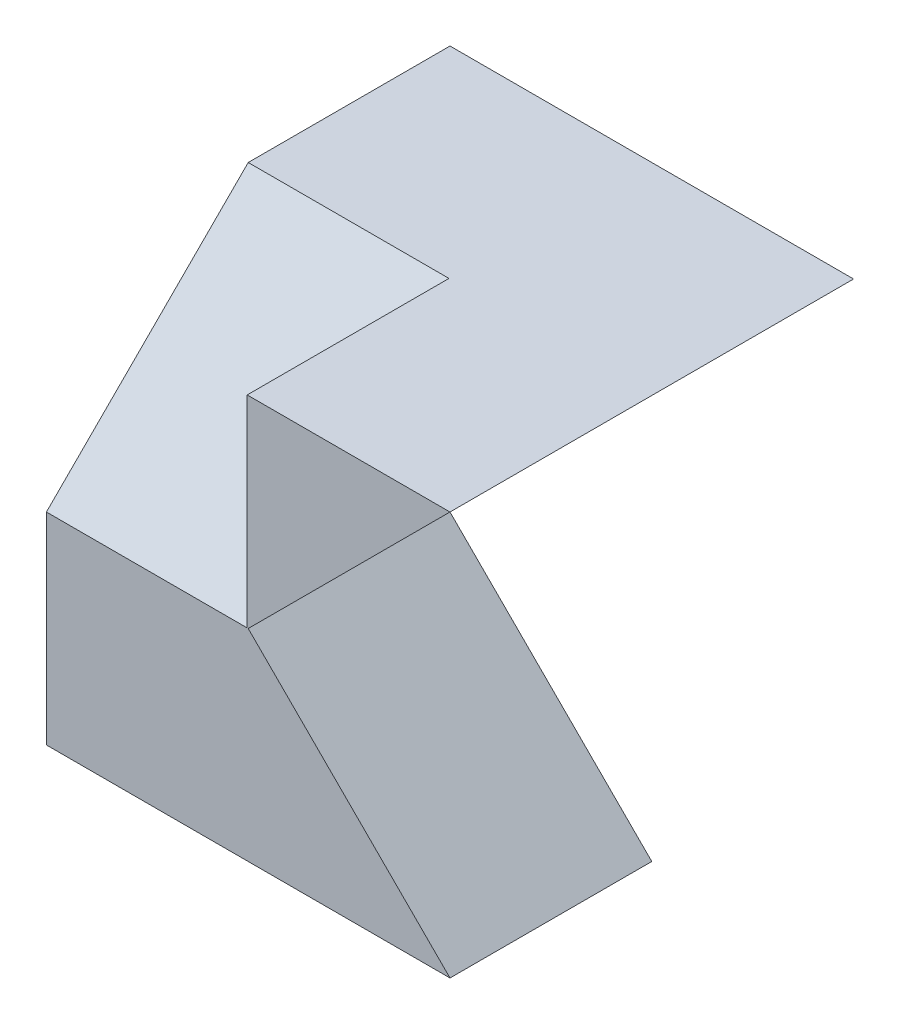
SolidWorks part; units mm, degrees
ref_plane "Front Plane" through (0, 0, 0) normal (0, 0, 1) x (1, 0, 0)
ref_plane "Top Plane" through (0, 0, 0) normal (0, 1, 0) x (1, 0, 0)
ref_plane "Right Plane" through (0, 0, 0) normal (1, 0, 0) x (0, 0, -1)
sketch "Sketch1" plane through (0, 0, 0) normal (0, 0, 1) x (1, 0, 0)
  line L0 (0, 0) -> (0, 4)
  line L1 (0, 4) -> (4, 4)
  line L2 (4, 4) -> (4, 0)
  line L3 (4, 0) -> (0, 0)
  dimension "D1" = 4
  dimension "D2" = 4
extrude "Boss-Extrude1" add sketch "Sketch1" along normal blind 4
sketch "Sketch2" plane through (0, 0, 4) normal (0, 0, 1) x (1, 0, 0)
  line L0 (4, 4) -> (2, 2)
  line L1 (2, 2) -> (4, 0)
  line L2 (4, 0) -> (4, 4)
  dimension "D1" = 2
extrude "Cut-Extrude1" cut sketch "Sketch2" against normal blind 4
sketch "Sketch5" plane through (0, 0, 0) normal (-1, 0, 0) x (0, 0, 1)
  line L0 (2, 4) -> (4, 2)
  line L1 (4, 4) -> (2, 4)
  line L2 (4, 4) -> (4, 2)
extrude "Cut-Extrude7" cut sketch "Sketch5" against normal blind 1.99
sketch "Sketch6" plane through (0, 0, 0) normal (-1, 0, 0) x (0, 0, 1)
  line L1 (0, 0) -> (2, 0)
  line L2 (0, 0) -> (0, 2)
  line L3 (0, 2) -> (2, 2)
  line L4 (2, 0) -> (2, 2)
  dimension "D1" = 2
  dimension "D2" = 2
extrude "Cut-Extrude8" cut sketch "Sketch6" against normal blind 21.99
